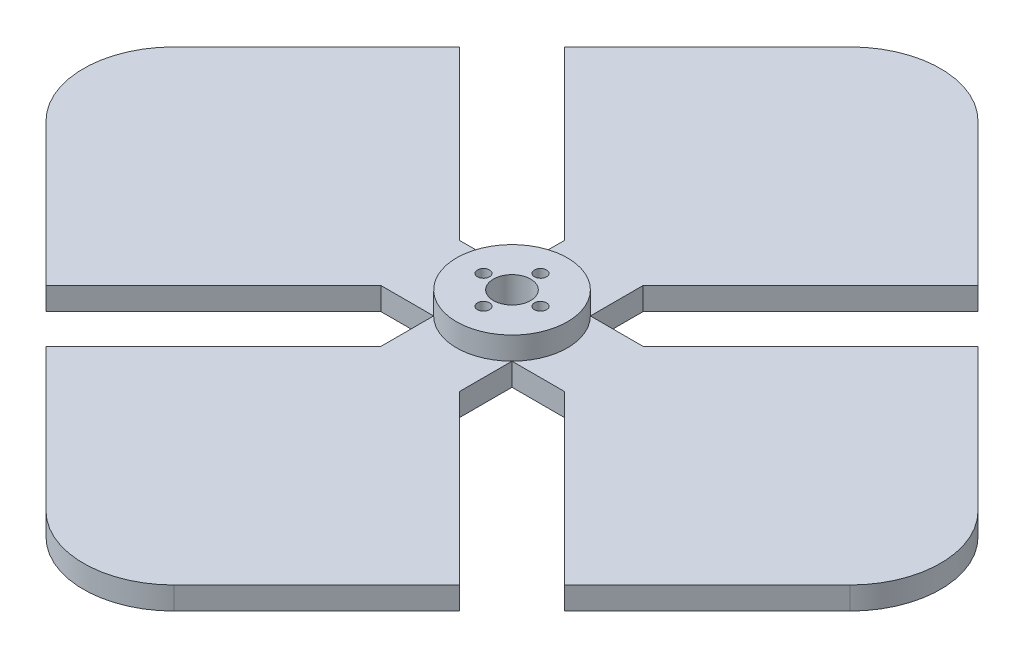
SolidWorks part; units mm, degrees
material "Perspex (TM) GS Acrylic Cast Sheet"
ref_plane "Front Plane" through (0, 0, 0) normal (0, 0, 1) x (1, 0, 0)
ref_plane "Top Plane" through (0, 0, 0) normal (0, 1, 0) x (1, 0, 0)
ref_plane "Right Plane" through (0, 0, 0) normal (1, 0, 0) x (0, 0, -1)
sketch "Sketch4" plane through (0, 0, 0) normal (0, 1, 0) x (1, 0, 0)
  line L8 (14.7955, 0) -> (72.808, -58.0125)
  line L9 (14.7955, 0) -> (72.808, 58.0125)
  line L10 (72.808, -58.0125) -> (130.8204, 0)
  line L11 (72.808, 58.0125) -> (130.8204, 0)
  line L13 (0, 11) -> (25.7955, 11)
  line L14 (0, 11) -> (0, -11)
  line L15 (0, -11) -> (25.7955, -11)
  line L16 (25.7955, 11) -> (25.7955, -11)
  dimension "D1" = 82.042
  dimension "D2" = 14.7955
  dimension "D3" = 22
extrude "Boss-Extrude5" add sketch "Sketch4" along normal blind 6.35 contours L9 L16 L8 L10 L11 | L16 L9 L8 | L14 L15 L8 L9 L13
sketch "Sketch6" plane through (0, 0, 0) normal (0, 0, 1) x (1, 0, 0)
  line L0 (0, 0) -> (0, 27.64) construction
fillet "Fillet1" radius 25.4 1 edges at (130.8204, 3.175, 0)
pattern_circular "CirPattern7" count 4 over 360 about axis through (0, 0, 0) along (0, 1, 0) of "Boss-Extrude5", "Fillet1"
sketch "Sketch13" plane through (0, 6.35, 0) normal (0, 1, 0) x (1, 0, 0)
  circle A0 centre (0, 0) radius 15.5563
extrude "Boss-Extrude8" add sketch "Sketch13" along normal blind 6.35
sketch "Sketch1" plane through (0, 0, 0) normal (0, 1, 0) x (1, 0, 0)
  circle A0 centre (0, 0) radius 2.6905 construction
  circle A1 centre (0, 0) radius 5.227
  circle A2 centre (8, 0) radius 1.6865
  circle A6 centre (0, -8) radius 1.6865
  circle A7 centre (-8, 0) radius 1.6865
  circle A8 centre (0, 8) radius 1.6865
  point P15 (0, 0)
  dimension "D1" = 10.454
  dimension "D3" = 3.373
  dimension "D2" = 8
extrude "Cut-Extrude1" cut sketch "Sketch1" along normal through all
equation "\"tightTol\"= 0.005in"
equation "\"normTol\"= 0.01in"
equation "\"looseTol\"= 0.02in"
equation "\"D1@Sketch1\"=\"normTol\"+10.2mm"
equation "\"D2@Sketch1\"=8mm"
equation "\"D1@Sketch4\"=3.25-\"looseTol\""
equation "\"D2@Sketch4\"=9/16+\"looseTol\""
equation "\"D3@Sketch1\"=3.5mm-\"tightTol\""
